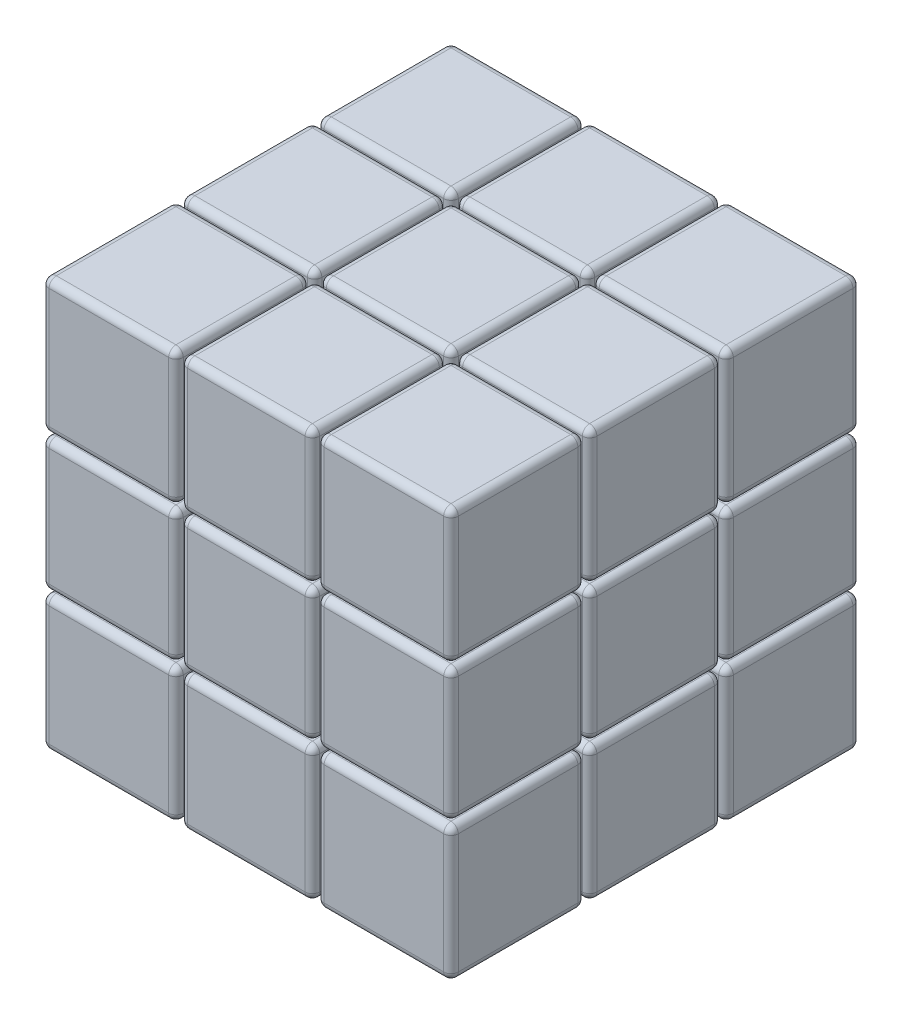
SolidWorks part; units mm, degrees
other "Camera1"
ref_plane "Front Plane" through (0, 0, 0) normal (0, 0, 1) x (1, 0, 0)
ref_plane "Top Plane" through (0, 0, 0) normal (0, 1, 0) x (1, 0, 0)
ref_plane "Right Plane" through (0, 0, 0) normal (1, 0, 0) x (0, 0, -1)
sketch "Sketch1" plane through (0, 0, 0) normal (0, 1, 0) x (1, 0, 0)
  line L1 (0, 0) -> (56, 0)
  line L2 (0, 0) -> (0, 56)
  line L3 (0, 56) -> (56, 56)
  line L4 (56, 0) -> (56, 56)
  line L5 (0, 0) -> (56, 56) construction
  line L6 (0, 56) -> (56, 0) construction
  point P4 (28, 28)
  dimension "D1" = 56
  dimension "D2" = 56
extrude "Boss-Extrude1" add sketch "Sketch1" along normal blind 56
sketch "Sketch2" plane through (0, 0, 0) normal (0, 0, 1) x (1, 0, 0)
  line L1 (0, 56) -> (56, 56) construction
  line L2 (0, 0) -> (56, 0) construction
  line L3 (37.6333, 18.9667) -> (56, 18.9667)
  line L4 (0, 56) -> (18.6667, 56) construction
  line L5 (18.6667, 56) -> (37.3333, 56) construction
  line L6 (37.3333, 56) -> (56, 56) construction
  line L7 (37.6333, 37.6333) -> (56, 37.6333)
  line L8 (0, 56) -> (0, 0) construction
  line L9 (56, 56) -> (56, 0) construction
  line L11 (0, 56) -> (0, 37.3333) construction
  line L12 (0, 37.3333) -> (0, 18.6667) construction
  line L13 (0, 18.6667) -> (0, 0) construction
  line L14 (18.9667, 37.6333) -> (37.0333, 37.6333)
  line L15 (18.3667, 56) -> (18.9667, 56)
  line L16 (18.3667, 56) -> (18.3667, 37.6333)
  line L17 (18.3667, 0) -> (18.9667, 0)
  line L18 (18.9667, 56) -> (18.9667, 37.6333)
  line L21 (37.0333, 56) -> (37.6333, 56)
  line L22 (37.0333, 56) -> (37.0333, 37.6333)
  line L23 (37.0333, 0) -> (37.6333, 0)
  line L24 (37.6333, 56) -> (37.6333, 37.6333)
  line L25 (18.9667, 18.9667) -> (37.0333, 18.9667)
  line L27 (0, 37.6333) -> (18.3667, 37.6333)
  line L28 (0, 37.6333) -> (0, 37.0333)
  line L29 (0, 37.0333) -> (18.3667, 37.0333)
  line L30 (56, 37.6333) -> (56, 37.0333)
  line L31 (37.6333, 18.3667) -> (37.6333, 0)
  line L32 (37.6333, 18.3667) -> (56, 18.3667)
  line L33 (0, 18.9667) -> (18.3667, 18.9667)
  line L34 (0, 18.9667) -> (0, 18.3667)
  line L35 (0, 18.3667) -> (18.3667, 18.3667)
  line L36 (56, 18.9667) -> (56, 18.3667)
  line L39 (37.6333, 37.0333) -> (37.6333, 18.9667)
  line L40 (18.3667, 37.0333) -> (18.3667, 18.9667)
  line L41 (18.9667, 37.0333) -> (37.0333, 37.0333)
  line L42 (18.9667, 37.0333) -> (18.9667, 18.9667)
  line L43 (18.9667, 18.3667) -> (18.9667, 0)
  line L44 (37.0333, 18.3667) -> (37.0333, 0)
  line L45 (37.6333, 37.0333) -> (56, 37.0333)
  line L46 (18.9667, 18.3667) -> (37.0333, 18.3667)
  line L48 (18.3667, 18.3667) -> (18.3667, 0)
  line L50 (37.0333, 37.0333) -> (37.0333, 18.9667)
  point P28 (18.6667, 28)
  point P31 (37.3333, 28)
  point P36 (28, 37.3333)
  point P41 (28, 18.6667)
  dimension "D1" = 0.3
  dimension "D2" = 0.3
  dimension "D5" = 0.3
  dimension "D6" = 0.3
  dimension "D7" = 0.3
  dimension "D8" = 0.3
extrude "Cut-Extrude1" cut sketch "Sketch2" against normal blind 56
sketch "Sketch3" plane through (0, 0, 0) normal (-1, 0, 0) x (0, 0, 1)
  line L0 (-37.3333, 56) -> (-37.3333, 0) construction
  line L1 (-56, 56) -> (0, 56) construction
  line L2 (-56, 0) -> (0, 0) construction
  line L3 (-18.6667, 56) -> (-18.6667, 0) construction
  line L4 (-56, 56) -> (-37.3333, 56) construction
  line L5 (-37.3333, 56) -> (-18.6667, 56) construction
  line L6 (-18.6667, 56) -> (0, 56) construction
  line L8 (-37.6333, 56) -> (-37.0333, 56)
  line L9 (-37.6333, 56) -> (-37.6333, 0)
  line L10 (-37.6333, 0) -> (-37.0333, 0)
  line L11 (-37.0333, 56) -> (-37.0333, 0)
  line L12 (-37.6333, 56) -> (-37.0333, 0) construction
  line L13 (-37.6333, 0) -> (-37.0333, 56) construction
  line L14 (-18.9667, 56) -> (-18.3667, 56)
  line L15 (-18.9667, 56) -> (-18.9667, 0)
  line L16 (-18.9667, 0) -> (-18.3667, 0)
  line L17 (-18.3667, 56) -> (-18.3667, 0)
  line L18 (-18.9667, 56) -> (-18.3667, 0) construction
  line L19 (-18.9667, 0) -> (-18.3667, 56) construction
  point P16 (-37.3333, 28)
  point P21 (-18.6667, 28)
  dimension "D1" = 0.3
  dimension "D2" = 0.3
  dimension "D3" = 0.3
  dimension "D4" = 0.3
extrude "Cut-Extrude2" cut sketch "Sketch3" against normal blind 56
fillet "Fillet2" radius 1 12 edges at (0, 46.8167, -18.3667) (9.1833, 56, 0) (0, 56, -9.1833) (9.1833, 56, -18.3667) (0, 37.6333, -9.1833) (18.3667, 46.8167, 0) (18.3667, 56, -9.1833) (18.3667, 46.8167, -18.3667) (9.1833, 37.6333, 0) (18.3667, 37.6333, -9.1833) (9.1833, 37.6333, -18.3667) (0, 46.8167, 0)
fillet "Fillet3" radius 1 12 edges at (9.1833, 18.3667, -37.0333) (9.1833, 18.3667, -18.9667) (0, 18.3667, -28) (18.3667, 18.3667, -28) (18.3667, 0, -28) (0, 0, -28) (18.3667, 9.1833, -37.0333) (18.3667, 9.1833, -18.9667) (9.1833, 0, -37.0333) (0, 9.1833, -37.0333) (9.1833, 0, -18.9667) (0, 9.1833, -18.9667)
fillet "Fillet4" radius 1 12 edges at (46.8167, 37.6333, -37.0333) (46.8167, 37.6333, -18.9667) (56, 37.6333, -28) (37.6333, 37.6333, -28) (56, 56, -28) (37.6333, 56, -28) (37.6333, 46.8167, -37.0333) (37.6333, 46.8167, -18.9667) (46.8167, 56, -37.0333) (56, 46.8167, -37.0333) (46.8167, 56, -18.9667) (56, 46.8167, -18.9667)
fillet "Fillet5" radius 1 12 edges at (18.9667, 28, -37.6333) (28, 37.0333, -37.6333) (37.0333, 28, -37.6333) (28, 18.9667, -37.6333) (18.9667, 18.9667, -46.8167) (18.9667, 28, -56) (18.9667, 37.0333, -46.8167) (28, 37.0333, -56) (37.0333, 37.0333, -46.8167) (37.0333, 28, -56) (37.0333, 18.9667, -46.8167) (28, 18.9667, -56)
fillet "Fillet6" radius 1 12 edges at (0, 9.1833, -37.6333) (9.1833, 0, -56) (18.3667, 9.1833, -56) (9.1833, 18.3667, -56) (9.1833, 18.3667, -37.6333) (0, 18.3667, -46.8167) (18.3667, 9.1833, -37.6333) (18.3667, 18.3667, -46.8167) (18.3667, 0, -46.8167) (9.1833, 0, -37.6333) (0, 9.1833, -56) (0, 0, -46.8167)
fillet "Fillet7" radius 1 12 edges at (46.8167, 56, 0) (37.6333, 56, -9.1833) (46.8167, 56, -18.3667) (56, 56, -9.1833) (56, 46.8167, 0) (56, 46.8167, -18.3667) (37.6333, 46.8167, 0) (37.6333, 37.6333, -9.1833) (37.6333, 46.8167, -18.3667) (46.8167, 37.6333, 0) (56, 37.6333, -9.1833) (46.8167, 37.6333, -18.3667)
fillet "Fillet8" radius 1 12 edges at (28, 37.6333, -37.0333) (28, 37.6333, -18.9667) (37.0333, 37.6333, -28) (37.0333, 56, -28) (18.9667, 37.6333, -28) (18.9667, 56, -28) (18.9667, 46.8167, -37.0333) (37.0333, 46.8167, -37.0333) (18.9667, 46.8167, -18.9667) (37.0333, 46.8167, -18.9667) (28, 56, -37.0333) (28, 56, -18.9667)
fillet "Fillet9" radius 1 12 edges at (28, 56, 0) (18.9667, 56, -9.1833) (28, 56, -18.3667) (18.9667, 46.8167, 0) (18.9667, 37.6333, -9.1833) (18.9667, 46.8167, -18.3667) (37.0333, 46.8167, 0) (37.0333, 56, -9.1833) (37.0333, 46.8167, -18.3667) (28, 37.6333, 0) (37.0333, 37.6333, -9.1833) (28, 37.6333, -18.3667)
fillet "Fillet10" radius 1 12 edges at (0, 28, -18.3667) (0, 18.9667, -9.1833) (9.1833, 37.0333, 0) (0, 37.0333, -9.1833) (9.1833, 37.0333, -18.3667) (18.3667, 28, 0) (18.3667, 37.0333, -9.1833) (18.3667, 28, -18.3667) (9.1833, 18.9667, 0) (18.3667, 18.9667, -9.1833) (9.1833, 18.9667, -18.3667) (0, 28, 0)
fillet "Fillet11" radius 1 12 edges at (46.8167, 18.9667, -56) (56, 28, -56) (46.8167, 37.0333, -56) (37.6333, 28, -56) (46.8167, 18.9667, -37.6333) (56, 18.9667, -46.8167) (37.6333, 28, -37.6333) (37.6333, 18.9667, -46.8167) (46.8167, 37.0333, -37.6333) (37.6333, 37.0333, -46.8167) (56, 28, -37.6333) (56, 37.0333, -46.8167)
fillet "Fillet12" radius 1 12 edges at (18.9667, 9.1833, -56) (28, 0, -56) (37.0333, 9.1833, -56) (28, 18.3667, -56) (28, 18.3667, -37.6333) (18.9667, 18.3667, -46.8167) (18.9667, 9.1833, -37.6333) (18.9667, 0, -46.8167) (37.0333, 9.1833, -37.6333) (37.0333, 18.3667, -46.8167) (37.0333, 0, -46.8167) (28, 0, -37.6333)
fillet "Fillet13" radius 1 12 edges at (28, 18.3667, -37.0333) (28, 18.3667, -18.9667) (18.9667, 18.3667, -28) (18.9667, 0, -28) (37.0333, 18.3667, -28) (37.0333, 0, -28) (37.0333, 9.1833, -37.0333) (18.9667, 9.1833, -37.0333) (37.0333, 9.1833, -18.9667) (18.9667, 9.1833, -18.9667) (28, 0, -37.0333) (28, 0, -18.9667)
fillet "Fillet14" radius 1 12 edges at (46.8167, 0, -56) (56, 9.1833, -56) (46.8167, 18.3667, -56) (37.6333, 9.1833, -56) (46.8167, 18.3667, -37.6333) (37.6333, 18.3667, -46.8167) (37.6333, 9.1833, -37.6333) (37.6333, 0, -46.8167) (56, 0, -46.8167) (56, 9.1833, -37.6333) (56, 18.3667, -46.8167) (46.8167, 0, -37.6333)
fillet "Fillet15" radius 1 12 edges at (37.0333, 28, -18.3667) (28, 37.0333, -18.3667) (18.9667, 28, -18.3667) (28, 18.9667, -18.3667) (37.0333, 18.9667, -9.1833) (37.0333, 37.0333, -9.1833) (18.9667, 37.0333, -9.1833) (18.9667, 18.9667, -9.1833) (28, 37.0333, 0) (37.0333, 28, 0) (28, 18.9667, 0) (18.9667, 28, 0)
fillet "Fillet16" radius 1 12 edges at (18.9667, 28, -37.0333) (18.9667, 28, -18.9667) (18.9667, 18.9667, -28) (18.9667, 37.0333, -28) (37.0333, 37.0333, -28) (37.0333, 18.9667, -28) (28, 18.9667, -37.0333) (37.0333, 28, -37.0333) (28, 37.0333, -37.0333) (28, 18.9667, -18.9667) (37.0333, 28, -18.9667) (28, 37.0333, -18.9667)
fillet "Fillet17" radius 1 12 edges at (0, 9.1833, -18.3667) (9.1833, 0, -18.3667) (0, 0, -9.1833) (18.3667, 0, -9.1833) (18.3667, 9.1833, 0) (18.3667, 18.3667, -9.1833) (18.3667, 9.1833, -18.3667) (9.1833, 18.3667, 0) (0, 18.3667, -9.1833) (9.1833, 18.3667, -18.3667) (0, 9.1833, 0) (9.1833, 0, 0)
fillet "Fillet18" radius 1 12 edges at (0, 46.8167, -37.6333) (9.1833, 56, -37.6333) (9.1833, 37.6333, -56) (18.3667, 46.8167, -56) (9.1833, 37.6333, -37.6333) (18.3667, 37.6333, -46.8167) (18.3667, 46.8167, -37.6333) (18.3667, 56, -46.8167) (0, 46.8167, -56) (0, 37.6333, -46.8167) (9.1833, 56, -56) (0, 56, -46.8167)
fillet "Fillet19" radius 1 12 edges at (46.8167, 18.9667, -37.0333) (46.8167, 18.9667, -18.9667) (56, 37.0333, -28) (37.6333, 37.0333, -28) (37.6333, 18.9667, -28) (56, 18.9667, -28) (46.8167, 37.0333, -37.0333) (37.6333, 28, -37.0333) (46.8167, 37.0333, -18.9667) (37.6333, 28, -18.9667) (56, 28, -37.0333) (56, 28, -18.9667)
fillet "Fillet20" radius 1 12 edges at (9.1833, 37.6333, -37.0333) (9.1833, 37.6333, -18.9667) (18.3667, 37.6333, -28) (18.3667, 56, -28) (0, 37.6333, -28) (0, 56, -28) (18.3667, 46.8167, -37.0333) (18.3667, 46.8167, -18.9667) (9.1833, 56, -37.0333) (0, 46.8167, -37.0333) (9.1833, 56, -18.9667) (0, 46.8167, -18.9667)
fillet "Fillet21" radius 1 12 edges at (46.8167, 56, -37.6333) (56, 46.8167, -56) (37.6333, 46.8167, -56) (46.8167, 37.6333, -56) (46.8167, 37.6333, -37.6333) (56, 37.6333, -46.8167) (37.6333, 46.8167, -37.6333) (37.6333, 37.6333, -46.8167) (56, 46.8167, -37.6333) (46.8167, 56, -56) (56, 56, -46.8167) (37.6333, 56, -46.8167)
fillet "Fillet22" radius 1 12 edges at (56, 28, 0) (56, 37.0333, -9.1833) (56, 28, -18.3667) (46.8167, 37.0333, 0) (37.6333, 37.0333, -9.1833) (46.8167, 37.0333, -18.3667) (37.6333, 28, 0) (37.6333, 18.9667, -9.1833) (37.6333, 28, -18.3667) (46.8167, 18.9667, 0) (56, 18.9667, -9.1833) (46.8167, 18.9667, -18.3667)
fillet "Fillet23" radius 1 12 edges at (28, 0, -18.3667) (37.0333, 0, -9.1833) (37.0333, 9.1833, 0) (37.0333, 18.3667, -9.1833) (37.0333, 9.1833, -18.3667) (18.9667, 9.1833, 0) (18.9667, 0, -9.1833) (18.9667, 9.1833, -18.3667) (28, 18.3667, 0) (18.9667, 18.3667, -9.1833) (28, 18.3667, -18.3667) (28, 0, 0)
fillet "Fillet24" radius 1 12 edges at (46.8167, 18.3667, -37.0333) (46.8167, 18.3667, -18.9667) (37.6333, 18.3667, -28) (37.6333, 0, -28) (56, 0, -28) (56, 18.3667, -28) (37.6333, 9.1833, -37.0333) (37.6333, 9.1833, -18.9667) (46.8167, 0, -37.0333) (56, 9.1833, -37.0333) (46.8167, 0, -18.9667) (56, 9.1833, -18.9667)
fillet "Fillet25" radius 1 12 edges at (46.8167, 0, -18.3667) (56, 9.1833, 0) (56, 18.3667, -9.1833) (56, 9.1833, -18.3667) (56, 0, -9.1833) (37.6333, 9.1833, 0) (37.6333, 0, -9.1833) (37.6333, 9.1833, -18.3667) (46.8167, 18.3667, 0) (37.6333, 18.3667, -9.1833) (46.8167, 18.3667, -18.3667) (46.8167, 0, 0)
fillet "Fillet26" radius 1 12 edges at (9.1833, 18.9667, -37.0333) (9.1833, 18.9667, -18.9667) (18.3667, 18.9667, -28) (18.3667, 37.0333, -28) (0, 37.0333, -28) (0, 18.9667, -28) (9.1833, 37.0333, -37.0333) (18.3667, 28, -37.0333) (9.1833, 37.0333, -18.9667) (18.3667, 28, -18.9667) (0, 28, -37.0333) (0, 28, -18.9667)
fillet "Fillet27" radius 1 12 edges at (28, 56, -37.6333) (18.9667, 46.8167, -56) (28, 37.6333, -56) (37.0333, 46.8167, -56) (28, 37.6333, -37.6333) (37.0333, 37.6333, -46.8167) (37.0333, 46.8167, -37.6333) (37.0333, 56, -46.8167) (18.9667, 46.8167, -37.6333) (18.9667, 37.6333, -46.8167) (28, 56, -56) (18.9667, 56, -46.8167)
fillet "Fillet28" radius 1 12 edges at (0, 28, -37.6333) (9.1833, 37.0333, -56) (9.1833, 18.9667, -56) (18.3667, 28, -56) (9.1833, 18.9667, -37.6333) (18.3667, 18.9667, -46.8167) (18.3667, 28, -37.6333) (18.3667, 37.0333, -46.8167) (9.1833, 37.0333, -37.6333) (0, 37.0333, -46.8167) (0, 28, -56) (0, 18.9667, -46.8167)
